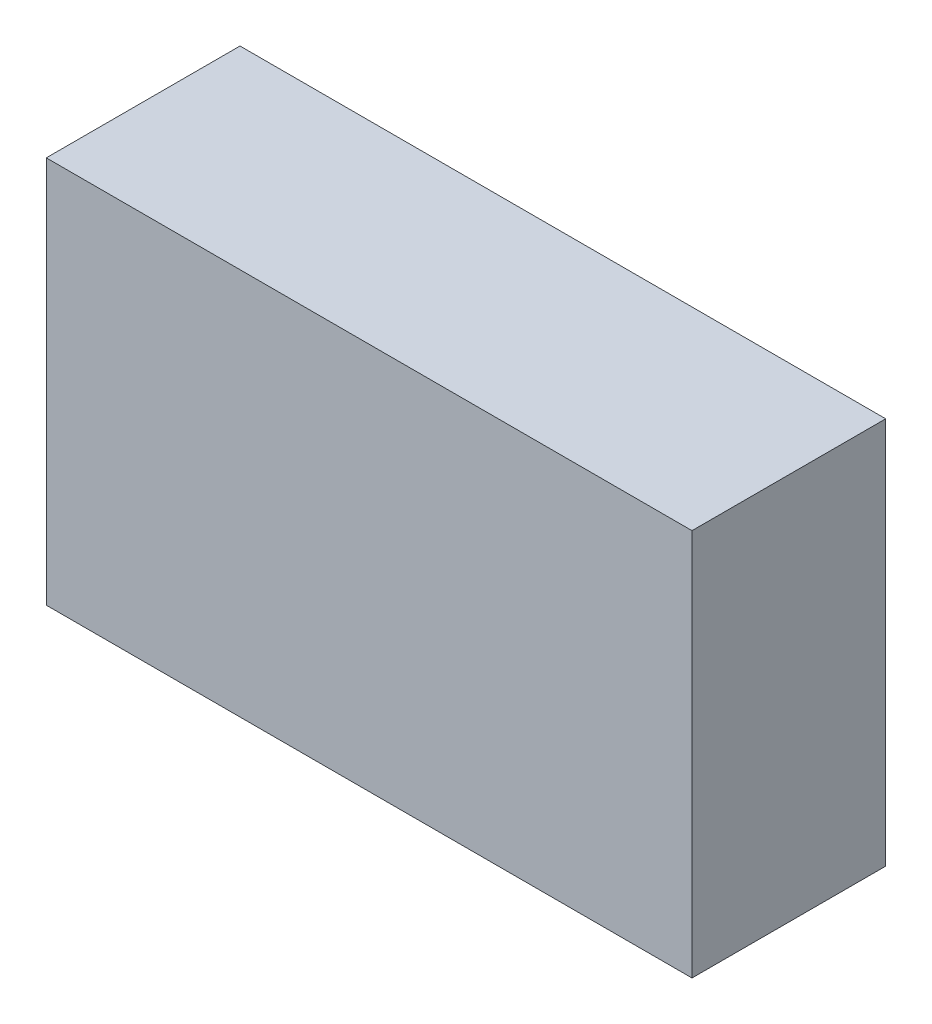
SolidWorks part; units mm, degrees
ref_plane "Front Plane" through (0, 0, 0) normal (0, 0, 1) x (1, 0, 0)
ref_plane "Top Plane" through (0, 0, 0) normal (0, 1, 0) x (1, 0, 0)
ref_plane "Right Plane" through (0, 0, 0) normal (1, 0, 0) x (0, 0, -1)
sketch "Sketch1" plane through (0, 0, 0) normal (0, 0, 1) x (1, 0, 0)
  line L1 (-10, 6) -> (10, 6)
  line L2 (-10, 6) -> (-10, -6)
  line L3 (-10, -6) -> (10, -6)
  line L4 (10, 6) -> (10, -6)
  line L5 (-10, 6) -> (10, -6) construction
  line L6 (-10, -6) -> (10, 6) construction
  point P0 (0, 0)
  dimension "D1" = 20
  dimension "D2" = 12
extrude "Boss-Extrude1" add sketch "Sketch1" along normal blind 6
